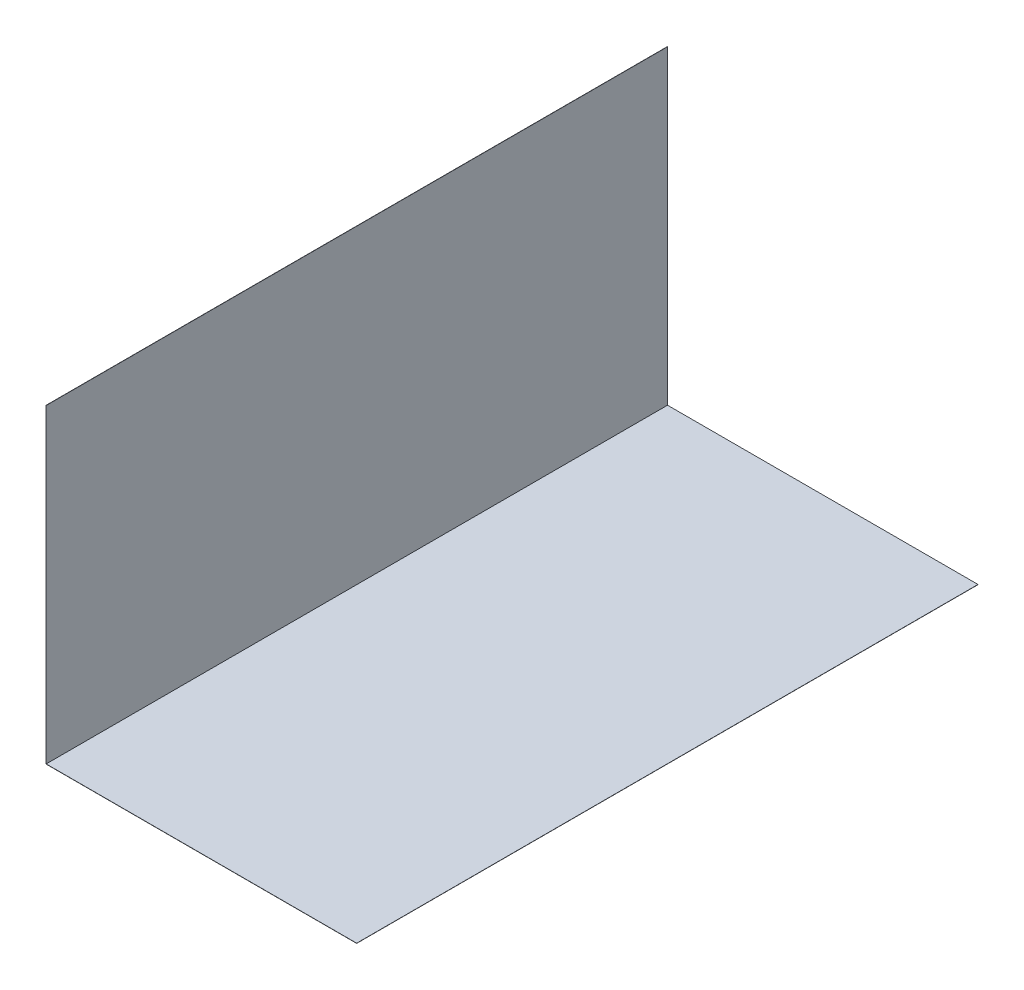
SolidWorks part; units mm, degrees
ref_plane "Front Plane" through (0, 0, 0) normal (0, 0, 1) x (1, 0, 0)
ref_plane "Top Plane" through (0, 0, 0) normal (0, 1, 0) x (1, 0, 0)
ref_plane "Right Plane" through (0, 0, 0) normal (1, 0, 0) x (0, 0, -1)
sketch "Sketch1" plane through (0, 0, 0) normal (0, 0, 1) x (1, 0, 0)
  line L0 (-7610, 7620) -> (-7610, -7610)
  line L2 (-7620, 7620) -> (-7620, -7620)
  line L3 (-7620, -7620) -> (7620, -7620)
  line L5 (-7610, -7610) -> (7620, -7610)
  line L6 (7620, -7610) -> (7620, -7620)
  line L7 (-7610, 7620) -> (-7620, 7620)
  point P0 (0, 0)
  dimension "D1" = 10
extrude "Boss-Extrude1" add sketch "Sketch1" along normal blind 30480
